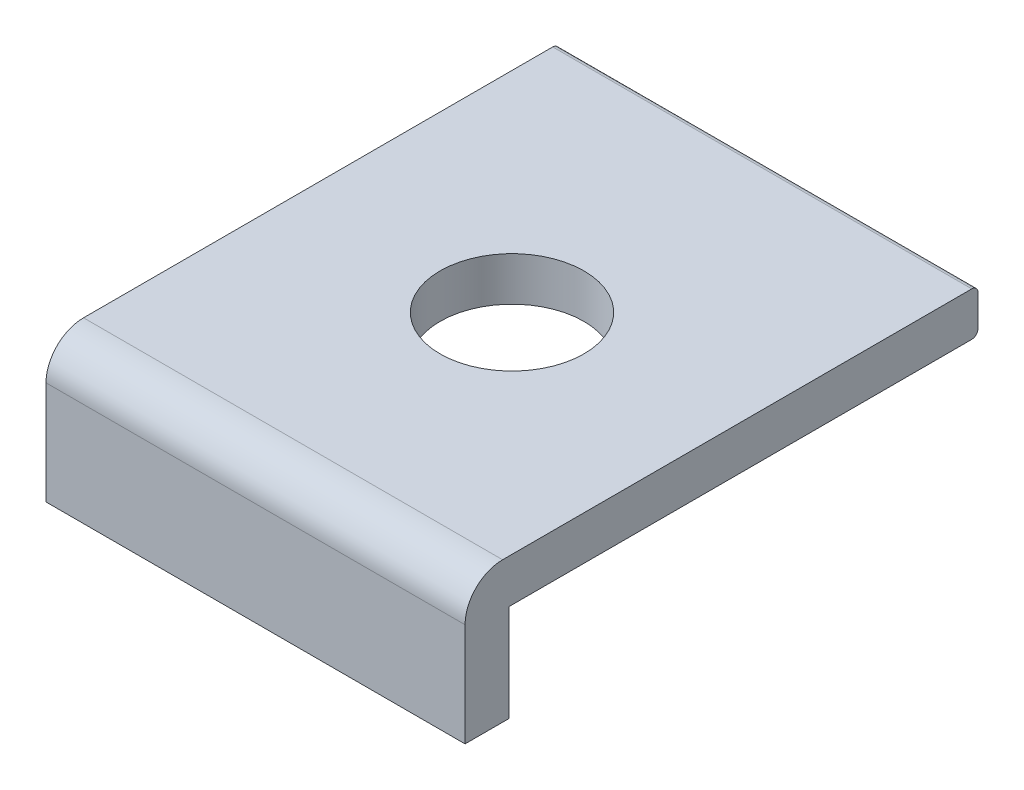
SolidWorks part; units mm, degrees
ref_plane "Plano frontal" through (0, 0, 0) normal (0, 0, 1) x (1, 0, 0)
ref_plane "Plano superior" through (0, 0, 0) normal (0, 1, 0) x (1, 0, 0)
ref_plane "Plano direito" through (0, 0, 0) normal (1, 0, 0) x (0, 0, -1)
sketch "Esboço4" plane through (0, 0, 0) normal (1, 0, 0) x (0, 0, -1)
  line L0 (0, 0) -> (0, 1.65)
  line L1 (0.6, 2.25) -> (8.101, 2.25)
  line L2 (8.201, 2.15) -> (8.201, 1.65)
  line L3 (0, 0) -> (0.7, 0)
  line L4 (0.7, 0) -> (0.7, 1.55)
  line L5 (0.7, 1.55) -> (8.101, 1.55)
  arc A0 (8.201, 1.65) -> (8.101, 1.55) centre (8.101, 1.65) cw
  arc A1 (8.201, 2.15) -> (8.101, 2.25) centre (8.101, 2.15) ccw
  arc A2 (0, 1.65) -> (0.6, 2.25) centre (0.6, 1.65) cw
  point P9 (8.201, 1.55)
  point P12 (8.201, 2.25)
  point P15 (0, 2.25)
  dimension "D5" = 0.1
  dimension "D6" = 0.6
  dimension "D1" = 2.25
  dimension "D2" = 8.201
  dimension "D3" = 0.7
  dimension "D4" = 0.7
extrude "Ressalto-extrusão12" add sketch "Esboço4" along normal blind 6.7
sketch "Esboço7" plane through (0, 2.25, 0) normal (0, 1, 0) x (1, 0, 0)
  circle A0 centre (3.35, 4.1005) radius 1.15
  dimension "D1" = 2.3
extrude "Corte-extrusão3" cut sketch "Esboço7" against normal blind 6.7
